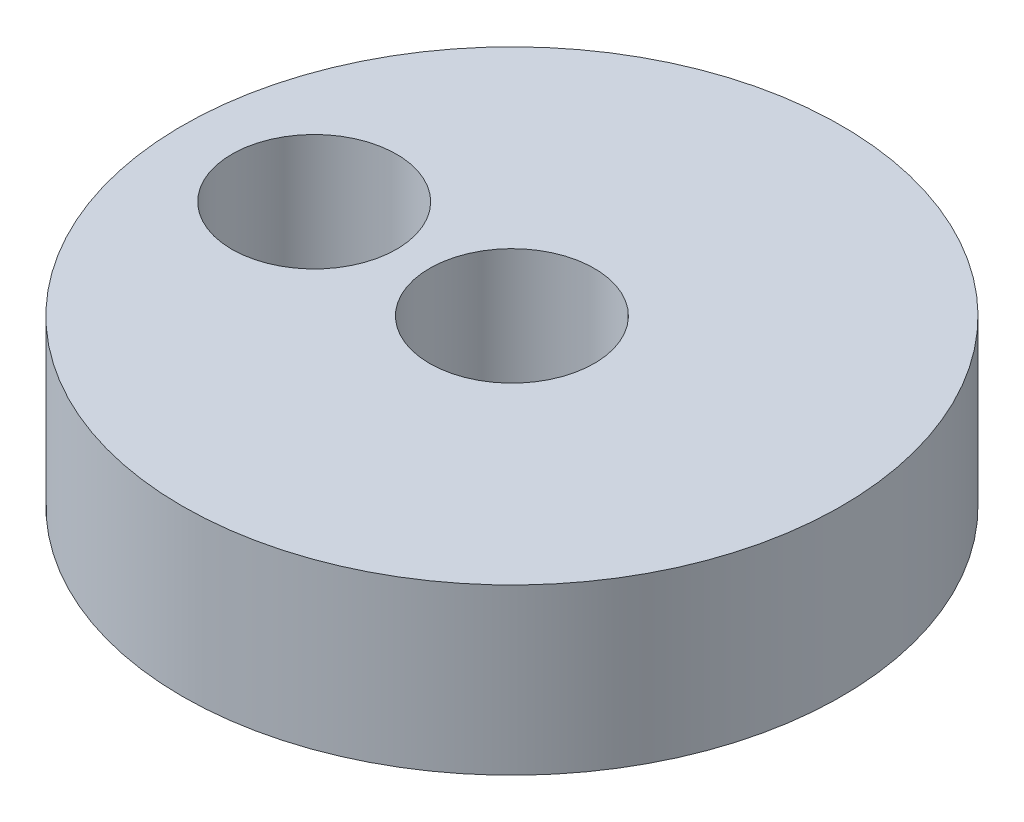
SolidWorks part; units mm, degrees
ref_plane "Front Plane" through (0, 0, 0) normal (0, 0, 1) x (1, 0, 0)
ref_plane "Top Plane" through (0, 0, 0) normal (0, 1, 0) x (1, 0, 0)
ref_plane "Right Plane" through (0, 0, 0) normal (1, 0, 0) x (0, 0, -1)
other "Center of Mass"
sketch "Sketch1" plane through (0, 0, 0) normal (0, 1, 0) x (1, 0, 0)
  circle A0 centre (0, 0) radius 5
  circle A1 centre (0, 0) radius 20
  dimension "D1" = 40
  dimension "D2" = 10
extrude "Boss-Extrude1" add sketch "Sketch1" along normal blind 10
sketch "Sketch4" plane through (0, 10, 0) normal (0, 1, 0) x (1, 0, 0)
  circle A0 centre (-12, 0) radius 5
  point P2 (0, 0)
  point P3 (0, 0)
  dimension "D1" = 10
  dimension "D2" = 12
extrude "Cut-Extrude1" cut sketch "Sketch4" against normal through all
sketch "Sketch5" plane through (0, 0, 0) normal (0, 1, 0) x (1, 0, 0)
  line L0 (0.8571, 0) -> (25.8571, 0)
  point P3 (1.0162, 0)
  dimension "D1" = 25
